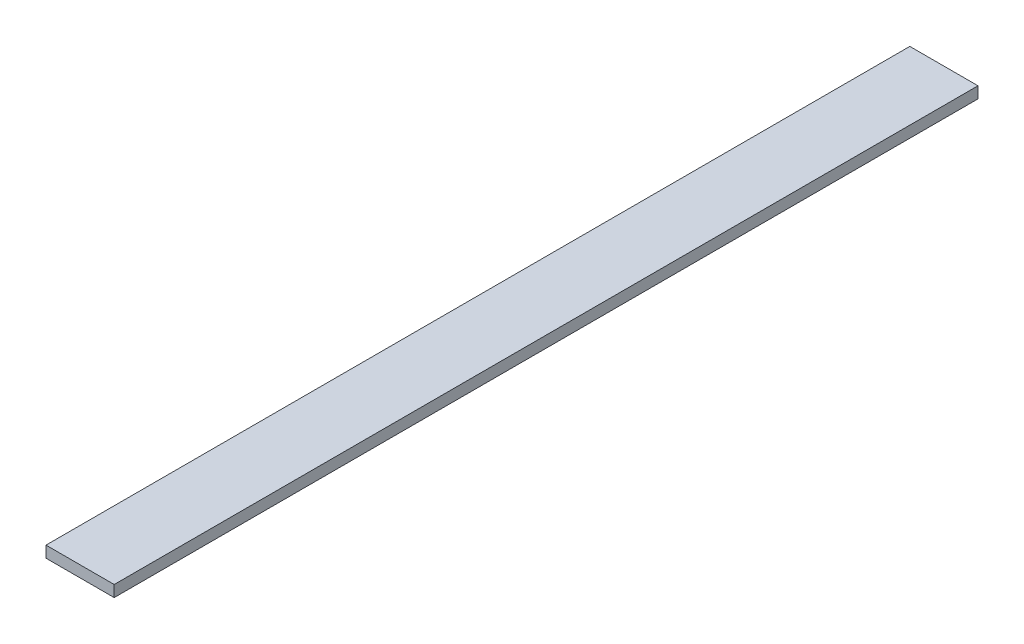
SolidWorks part; units mm, degrees
ref_plane "Front Plane" through (0, 0, 0) normal (0, 0, 1) x (1, 0, 0)
ref_plane "Top Plane" through (0, 0, 0) normal (0, 1, 0) x (1, 0, 0)
ref_plane "Right Plane" through (0, 0, 0) normal (1, 0, 0) x (0, 0, -1)
sketch "Sketch1" plane through (0, 0, 0) normal (0, 0, 1) x (1, 0, 0)
  line L1 (0, 0) -> (19.05, 0)
  line L2 (0, 0) -> (0, 3.175)
  line L3 (0, 3.175) -> (19.05, 3.175)
  line L4 (19.05, 0) -> (19.05, 3.175)
  dimension "D1" = 19.05
  dimension "D2" = 3.175
extrude "Boss-Extrude1" add sketch "Sketch1" along normal blind 241.3
